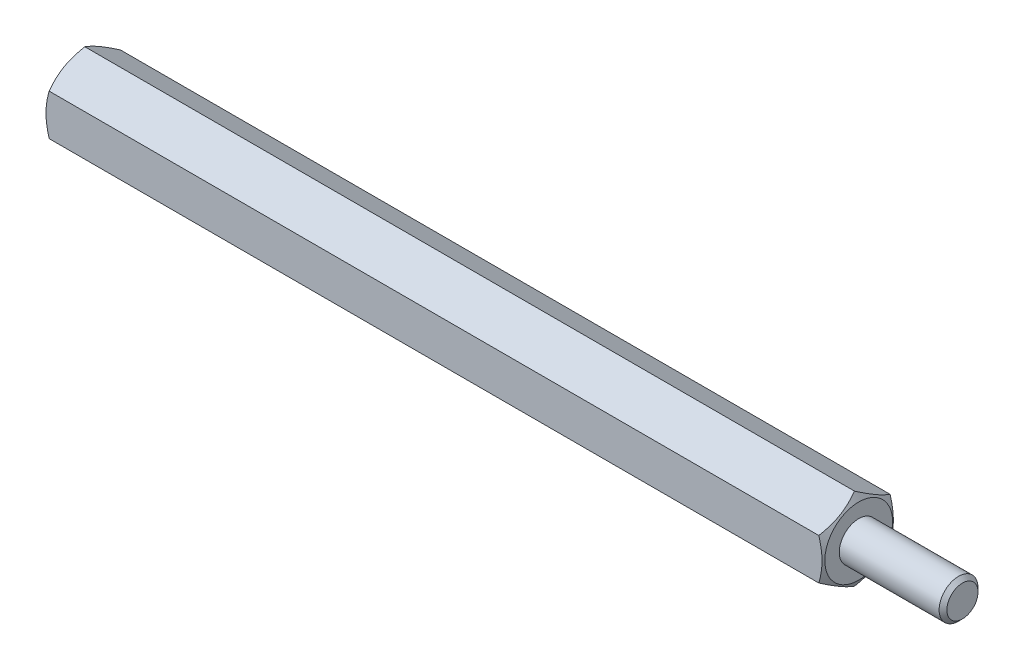
SolidWorks part; units mm, degrees
material "Brass"
ref_plane "Front Plane" through (0, 0, 0) normal (0, 0, 1) x (1, 0, 0)
ref_plane "Top Plane" through (0, 0, 0) normal (0, 1, 0) x (1, 0, 0)
ref_plane "Right Plane" through (0, 0, 0) normal (1, 0, 0) x (0, 0, -1)
sketch "Sketch1" plane through (0, 0, 0) normal (1, 0, 0) x (0, 0, -1)
  line L1 (0, 3.1754) -> (-2.75, 1.5877)
  line L2 (-2.75, 1.5877) -> (-2.75, -1.5877)
  line L3 (-2.75, -1.5877) -> (0, -3.1754)
  line L4 (0, -3.1754) -> (2.75, -1.5877)
  line L5 (2.75, -1.5877) -> (2.75, 1.5877)
  line L6 (2.75, 1.5877) -> (0, 3.1754)
  circle A0 centre (0, 0) radius 2.75 construction
extrude "Boss-Extrude1" add sketch "Sketch1" along normal blind 60
sketch "Sketch2" plane through (60, 0, 0) normal (1, 0, 0) x (0, 0, -1)
  circle A0 centre (0, 0) radius 1.5
extrude "Boss-Extrude2" add sketch "Sketch2" along normal blind 8
sketch "Sketch3" plane through (0, 0, 0) normal (-1, 0, 0) x (0, 0, 1)
  circle A0 centre (0, 0) radius 1.5
extrude "Cut-Extrude1" cut sketch "Sketch3" against normal blind 10
sketch "Sketch4" plane through (0, 0, 0) normal (0, 1, 0) x (1, 0, 0)
  line L0 (0, 0) -> (0, 2.6125)
  line L1 (0, 2.6125) -> (4.3921, 10.2198)
  line L2 (0, 2.6125) -> (0, 10.2198)
  line L3 (0, 10.2198) -> (4.3921, 10.2198)
  line L4 (0, 0) -> (-8.2035, 0) construction
  line L5 (60, 0) -> (60, 2.6125)
  line L6 (60, 2.6125) -> (55.6079, 10.2198)
  line L7 (60, 2.6125) -> (60, 10.2198)
  line L8 (60, 10.2198) -> (55.6079, 10.2198)
  line L9 (0, 0) -> (60, 0)
  dimension "D1" = 60
revolve "Cut-Revolve1" cut sketch "Sketch4" angle 360 about L4
chamfer "Chamfer1" distance 0.3 angle 45 1 edges at (68, 0, -1.5)
